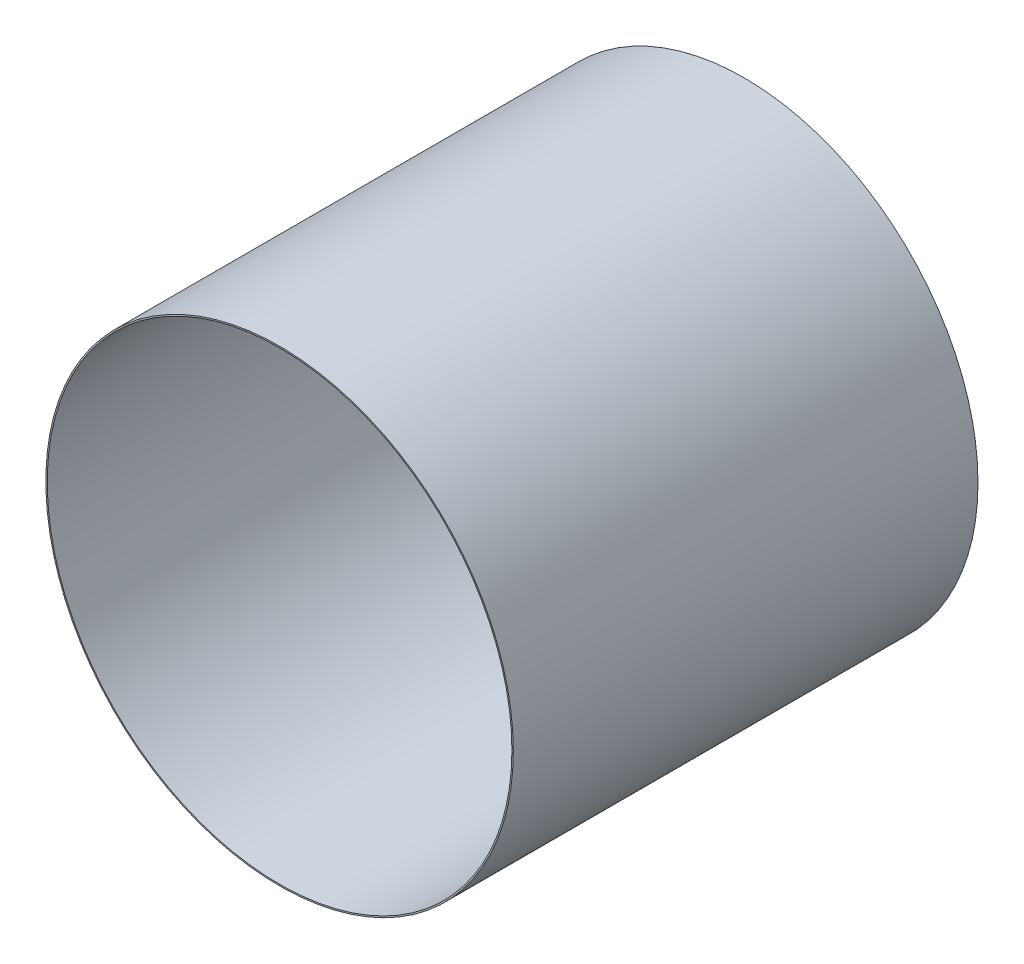
SolidWorks part; units mm, degrees
ref_plane "Front" through (0, 0, 0) normal (0, 0, 1) x (1, 0, 0)
ref_plane "Top" through (0, 0, 0) normal (0, 1, 0) x (1, 0, 0)
ref_plane "Right" through (0, 0, 0) normal (1, 0, 0) x (0, 0, -1)
sketch "Sketch1" plane through (0, 0, 0) normal (0, 0, 1) x (1, 0, 0)
  circle A0 centre (0, 0) radius 38.3273
  dimension "D1" = 76.6547
extrude "Boss-Extrude1" add sketch "Sketch1" against normal blind 76.2
sketch "Sketch2" plane through (0, 0, 0) normal (0, 0, 1) x (1, 0, 0)
  circle A0 centre (0, 0) radius 38.1
  dimension "D1" = 76.2
extrude "Cut-Extrude1" cut sketch "Sketch2" against normal blind 76.2
sketch "Sketch3" plane through (0, 0, 0) normal (0, 1, 0) x (1, 0, 0)
  line L0 (0, 0) -> (0, 76.2) construction
  line L1 (38.1, 76.2) -> (-38.1, 76.2) construction
ref_plane "Back Plane" through (0, 0, -76.2) normal (0, 0, 1) x (1, 0, 0)
